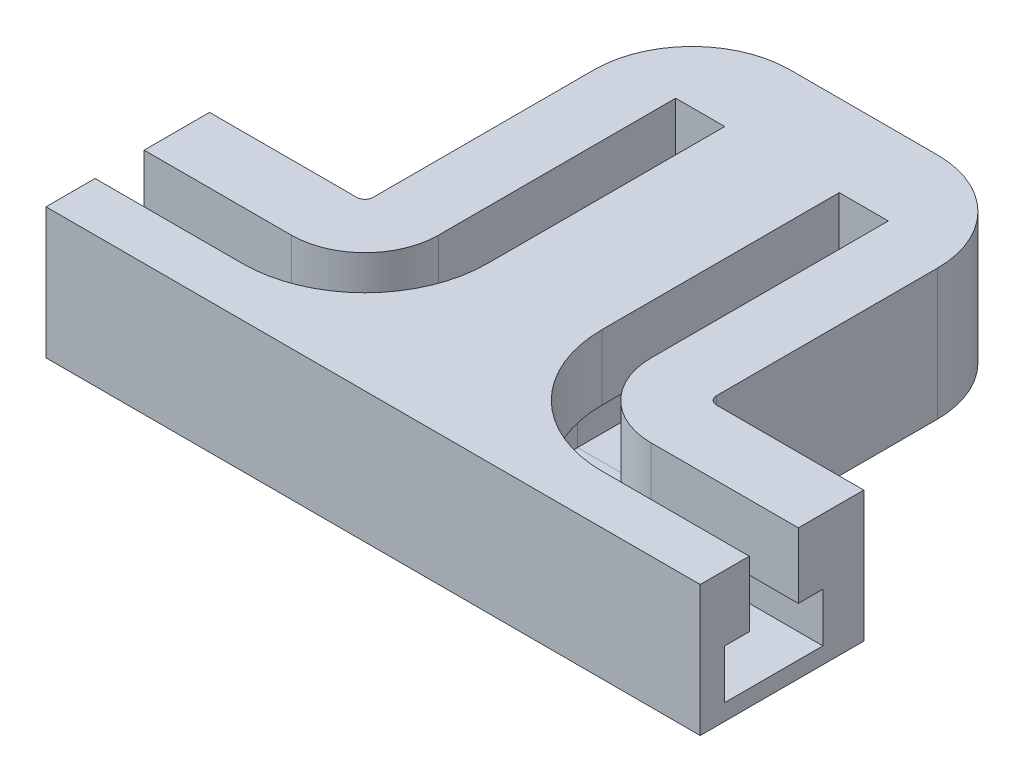
SolidWorks part; units mm, degrees
ref_plane "Front Plane" through (0, 0, 0) normal (0, 0, 1) x (1, 0, 0)
ref_plane "Top Plane" through (0, 0, 0) normal (0, 1, 0) x (1, 0, 0)
ref_plane "Right Plane" through (0, 0, 0) normal (1, 0, 0) x (0, 0, -1)
sketch "Sketch1" plane through (0, 0, 0) normal (0, 0, 1) x (1, 0, 0)
  line L1 (0, 0) -> (-100, 0)
  line L2 (0, 0) -> (0, 40)
  line L3 (0, 40) -> (-100, 40)
  line L4 (-100, 0) -> (-100, 40)
  dimension "D1" = 40
  dimension "D2" = 100
extrude "Boss-Extrude1" add sketch "Sketch1" along normal blind 150
sketch "Sketch2" plane through (-100, 0, 0) normal (-1, 0, 0) x (0, 0, 1)
  line L0 (150, 40) -> (0, 40) construction
  line L1 (135, 40) -> (120, 40)
  line L2 (135, 40) -> (135, 20)
  line L3 (150, 40) -> (150, 0) construction
  line L4 (120, 40) -> (120, 20)
  line L5 (120, 20) -> (112.5, 20)
  line L6 (142.5, 20) -> (135, 20)
  line L7 (142.5, 20) -> (142.5, 5)
  line L8 (142.5, 5) -> (112.5, 5)
  line L9 (112.5, 20) -> (112.5, 5)
  dimension "D1" = 15
  dimension "D2" = 30
  dimension "D3" = 20
  dimension "D4" = 15
  dimension "D5" = 15
sketch "Sketch3" plane through (0, 40, 0) normal (0, 1, 0) x (1, 0, 0)
  line L0 (-100, -127.5) -> (-55, -127.5)
  line L1 (-100, -142.5) -> (-100, -112.5) construction
  line L2 (-25, -97.5) -> (-25, -25)
  line L3 (0, 0) -> (-100, 0) construction
  line L4 (0, -150) -> (0, 0) construction
  arc A0 (-55, -127.5) -> (-25, -97.5) centre (-55, -97.5) ccw
  dimension "D1" = 30
  dimension "D2" = 25
  dimension "D3" = 25
sweep "Cut-Sweep1" cut profiles "Sketch2" path "Sketch3"
sketch "Sketch4" plane through (0, 40, 0) normal (0, 1, 0) x (1, 0, 0)
  line L4 (-52.5, -25) -> (-52.5, 0)
  line L5 (0, 0) -> (-100, 0) construction
  line L6 (-100, -100) -> (-55, -100)
  line L7 (-52.5, -97.5) -> (-52.5, -25)
  line L8 (-100, -100) -> (-55, -100)
  line L9 (-52.5, -97.5) -> (-52.5, -25)
  line L10 (-100, -120) -> (-100, 0) construction
  line L11 (-100, -100) -> (-100, 0)
  line L12 (-52.5, 0) -> (-100, 0)
  arc A3 (-55, -100) -> (-52.5, -97.5) centre (-55, -97.5) ccw
  arc A4 (-55, -100) -> (-52.5, -97.5) centre (-55, -97.5) ccw
  dimension "D1" = 20
extrude "Cut-Extrude1" cut sketch "Sketch4" against normal through all
fillet "Fillet1" radius 30 1 edges at (-52.5, 20, 0)
mirror "Mirror1" about plane through (0, 0, 150) normal (-1, 0, 0) of "Fillet1", "Cut-Extrude1", "Cut-Sweep1", "Boss-Extrude1"
